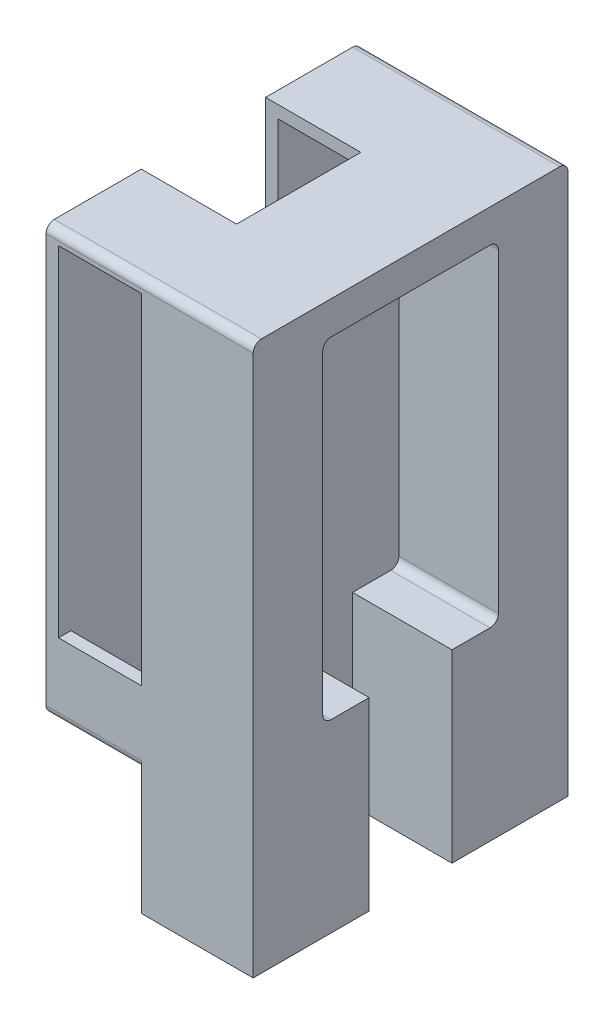
SolidWorks part; units mm, degrees
ref_plane "Front Plane" through (0, 0, 0) normal (0, 0, 1) x (1, 0, 0)
ref_plane "Top Plane" through (0, 0, 0) normal (0, 1, 0) x (1, 0, 0)
ref_plane "Right Plane" through (0, 0, 0) normal (1, 0, 0) x (0, 0, -1)
sketch "Sketch1" plane through (0, 0, 0) normal (0, 0, 1) x (1, 0, 0)
  line L0 (0, 0) -> (31.75, 0)
  line L1 (31.75, 0) -> (31.75, -84.2142)
  line L2 (31.75, -84.2142) -> (0, -84.2142)
  line L3 (0, -84.2142) -> (0, 0)
extrude "Boss-Extrude1" add sketch "Sketch1" against normal blind 46.355 and the other way blind 1.905
sketch "Sketch2" plane through (0, 0, 1.905) normal (0, 0, 1) x (1, 0, 0)
  line L0 (0, 0) -> (0, -1.905)
  line L1 (0, 0) -> (0, -84.2142) construction
  line L2 (0, -1.905) -> (1.905, -1.905)
sketch "Sketch3" plane through (0, 0, 1.905) normal (0, 0, 1) x (1, 0, 0)
  line L0 (1.905, -1.905) -> (14.605, -1.905)
  line L1 (14.605, -1.905) -> (14.605, -53.975)
  line L2 (14.605, -53.975) -> (1.905, -53.975)
  line L3 (1.905, -53.975) -> (1.905, -1.905)
  line L4 (0, -84.2142) -> (14.605, -84.2142)
  line L5 (0, -84.2142) -> (31.75, -84.2142) construction
  line L6 (14.605, -84.2142) -> (14.605, -65.1642)
  line L7 (14.605, -65.1642) -> (0, -65.1642)
  line L8 (0, 0) -> (0, -84.2142) construction
  line L9 (0, -65.1642) -> (0, -84.2142)
extrude "Cut-Extrude1" cut sketch "Sketch3" against normal through all
sketch "Sketch4" plane through (0, 0, 0) normal (0, 1, 0) x (1, 0, 0)
  line L7 (1.905, 22.225) -> (1.905, 31.75)
  line L8 (1.905, 31.75) -> (14.4052, 31.75)
  line L9 (14.4052, 31.75) -> (14.4052, 12.7)
  line L10 (14.4052, 12.7) -> (1.905, 12.7)
  line L11 (1.905, 12.7) -> (1.905, 22.225)
extrude "Cut-Extrude2" cut sketch "Sketch4" along direction (0, 1, 0) on the side against the normal blind 65.405
sketch "Sketch5" plane through (0, 0, 0) normal (-1, 0, 0) x (0, 0, 1)
  line L0 (-22.225, 0) -> (-12.7, 0)
  line L1 (-46.355, 0) -> (1.905, 0) construction
  line L2 (-12.7, 0) -> (-12.7, -52.705)
  line L3 (-12.7, -52.705) -> (-31.75, -52.705)
  line L4 (-31.75, -52.705) -> (-31.75, 0)
  line L5 (-31.75, 0) -> (-22.225, 0)
extrude "Cut-Extrude3" cut sketch "Sketch5" against normal up to surface (14.605 mm away) up to face at (14.605, -27.94, -22.225)
sketch "Sketch6" plane through (0, -65.1642, 0) normal (0, -1, 0) x (1, 0, 0)
  line L0 (1.905, -22.225) -> (1.905, 0)
  line L1 (1.905, -31.75) -> (1.905, -12.7) construction
  line L2 (1.905, 0) -> (14.605, 0)
  line L3 (14.605, -46.355) -> (14.605, 1.905) construction
  line L4 (14.605, 0) -> (14.605, -44.45)
  line L5 (14.605, -44.45) -> (1.905, -44.45)
  line L6 (1.905, -44.45) -> (1.905, -22.225)
extrude "Cut-Extrude4" cut sketch "Sketch6" against normal up to next
sketch "Sketch7" plane through (31.75, 0, 0) normal (1, 0, 0) x (0, 0, -1)
  line L2 (22.225, -5.08) -> (35.687, -5.08)
  line L3 (35.687, -5.08) -> (35.687, -55.88)
  line L4 (35.687, -55.88) -> (28.575, -55.88)
  line L5 (28.575, -55.88) -> (28.575, -84.2142)
  line L6 (-1.905, -84.2142) -> (46.355, -84.2142) construction
  line L7 (28.575, -84.2142) -> (15.875, -84.2142)
  line L8 (15.875, -84.2142) -> (15.875, -55.88)
  line L9 (15.875, -55.88) -> (8.763, -55.88)
  line L10 (8.763, -55.88) -> (8.763, -5.08)
  line L11 (8.763, -5.08) -> (22.225, -5.08)
extrude "Cut-Extrude5" cut sketch "Sketch7" against normal blind 15.24
sketch "Sketch8" plane through (16.51, 0, 0) normal (1, 0, 0) x (0, 0, -1)
  circle A0 centre (33.655, -7.62) radius 1.016
  circle A1 centre (10.795, -7.62) radius 1.016
extrude "Boss-Extrude2" add sketch "Sketch8" along normal blind 5.08
fillet "Fillet1" radius 1.27 4 edges at (24.13, -55.88, -8.763) (24.13, -55.88, -35.687) (24.13, -5.08, -8.763) (24.13, -5.08, -35.687)
fillet "Fillet2" radius 1.27 4 edges at (15.875, 0, -46.355) (15.875, 0, 1.905) (7.3025, -65.1642, -46.355) (7.3025, -65.1642, 1.905)
